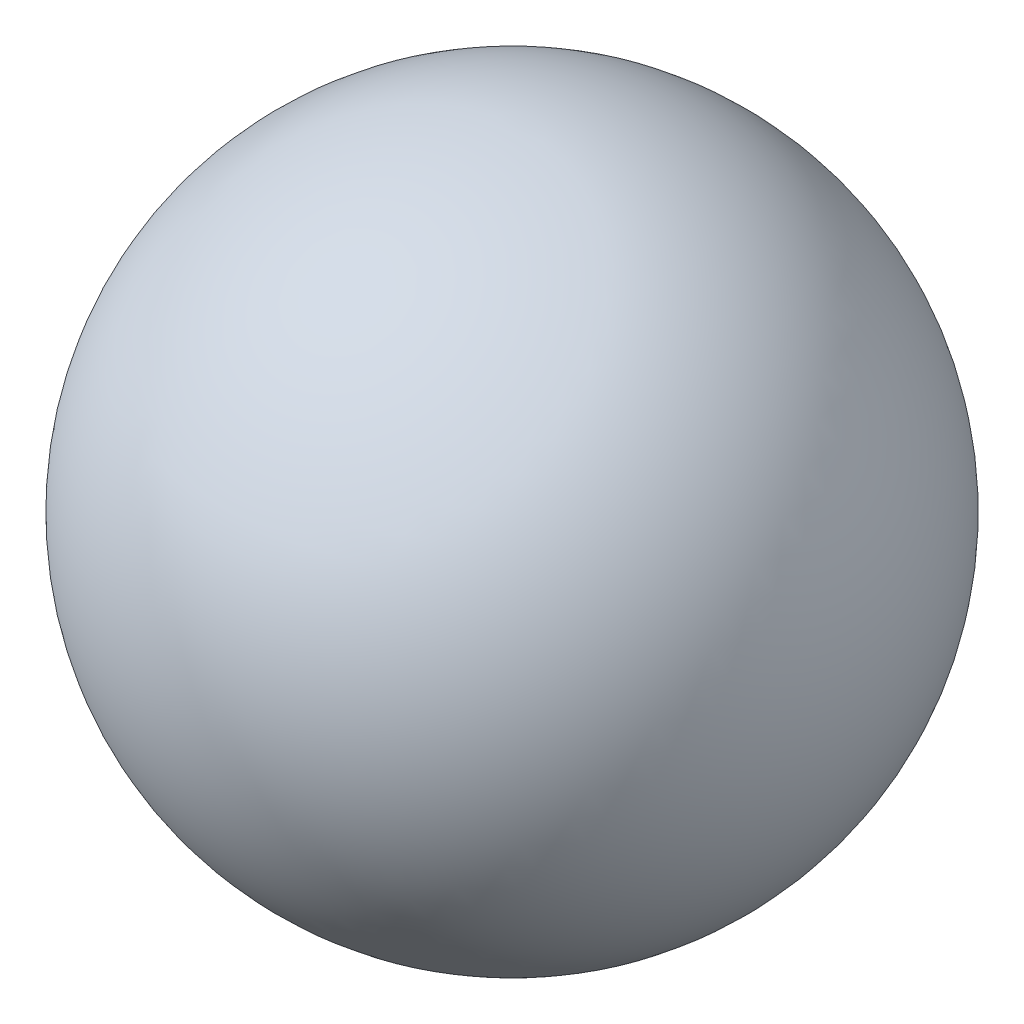
SolidWorks part; units mm, degrees
material "Tungsten"
ref_plane "Front Plane" through (0, 0, 0) normal (0, 0, 1) x (1, 0, 0)
ref_plane "Top Plane" through (0, 0, 0) normal (0, 1, 0) x (1, 0, 0)
ref_plane "Right Plane" through (0, 0, 0) normal (1, 0, 0) x (0, 0, -1)
sketch "Sketch1" plane through (0, 0, 0) normal (0, 0, 1) x (1, 0, 0)
  line L0 (0, 1.5) -> (0, -1.5)
  arc A0 (0, -1.5) -> (0, 1.5) centre (0, 0) ccw
  dimension "D1" = 3
revolve "Revolve1" add sketch "Sketch1" angle 360 about L0
